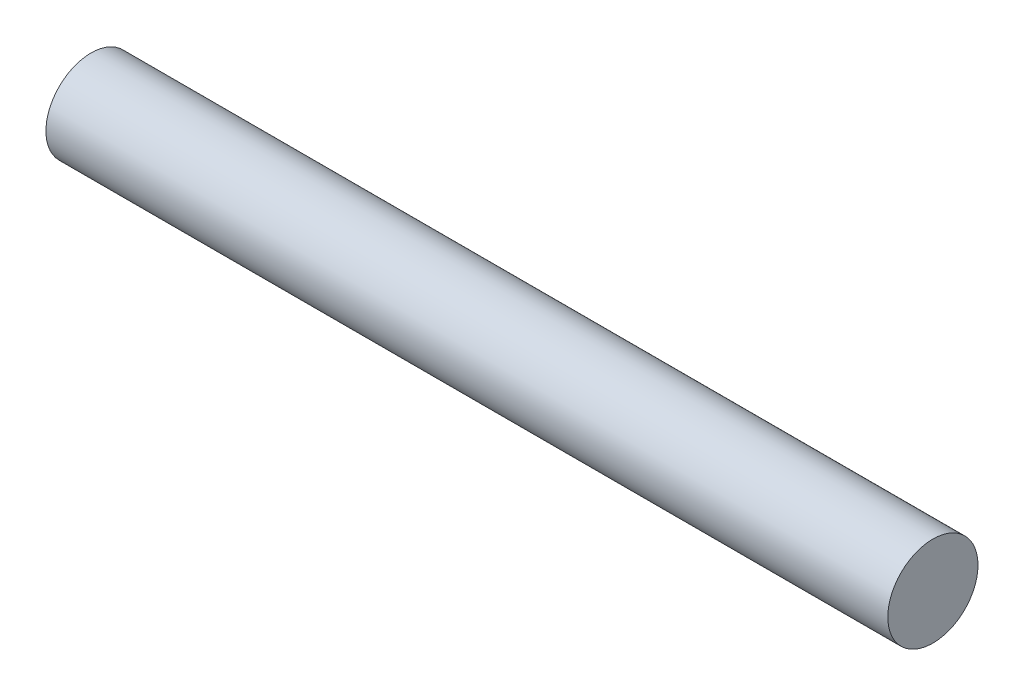
SolidWorks part; units mm, degrees
ref_plane "Alzado" through (0, 0, 0) normal (0, 0, 1) x (1, 0, 0)
ref_plane "Planta" through (0, 0, 0) normal (0, 1, 0) x (1, 0, 0)
ref_plane "Vista lateral" through (0, 0, 0) normal (1, 0, 0) x (0, 0, -1)
sketch "Croquis1" plane through (0, 0, 0) normal (0, 0, 1) x (1, 0, 0)
  line L0 (0, 0) -> (177.8, 0)
  dimension "D1" = 177.8
sketch "Croquis2" plane through (0, 0, 0) normal (1, 0, 0) x (0, 0, -1)
  circle A0 centre (0, 0) radius 9.525
  dimension "D1" = 19.05
sweep "Barrer1" add profiles "Croquis2" path "Croquis1"
ref_plane "Plano1" through (88.9, 0, 0) normal (-1, 0, 0) x (0, 0, 1)
